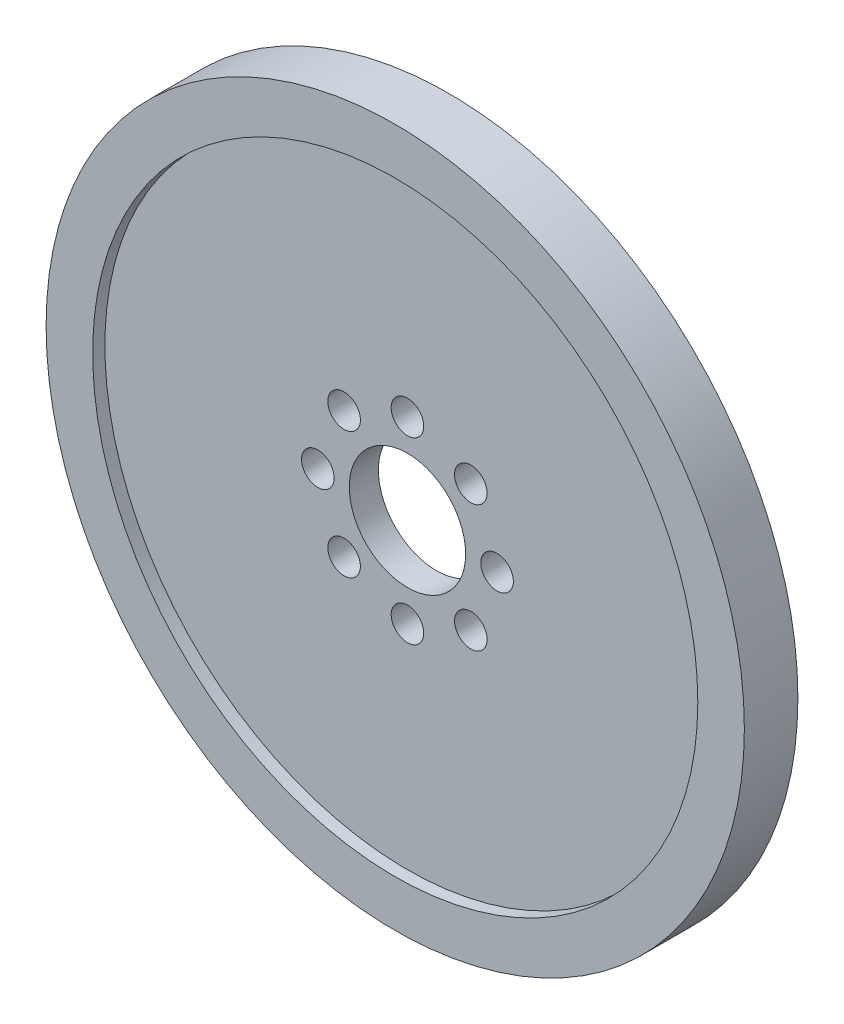
SolidWorks part; units mm, degrees
ref_plane "Front Plane" through (0, 0, 0) normal (0, 0, 1) x (1, 0, 0)
ref_plane "Top Plane" through (0, 0, 0) normal (0, 1, 0) x (1, 0, 0)
ref_plane "Right Plane" through (0, 0, 0) normal (1, 0, 0) x (0, 0, -1)
sketch "Sketch1" plane through (0, 0, 0) normal (0, 0, 1) x (1, 0, 0)
  circle A0 centre (0, 0) radius 38.1
  circle A1 centre (0, 0) radius 33.02
  dimension "D1" = 76.2
  dimension "D2" = 66.04
extrude "Boss-Extrude1" add sketch "Sketch1" along normal mid plane 5.842
sketch "Sketch3" plane through (0, 0, 0) normal (0, 0, 1) x (1, 0, 0)
  circle A0 centre (0, 0) radius 33.02
  circle A1 centre (0, 0) radius 6.35
  circle A2 centre (0, 9.779) radius 1.778
  circle A3 centre (6.9148, 6.9148) radius 1.778
  circle A4 centre (9.779, 0) radius 1.778
  circle A5 centre (6.9148, -6.9148) radius 1.778
  circle A6 centre (0, -9.779) radius 1.778
  circle A7 centre (-6.9148, -6.9148) radius 1.778
  circle A8 centre (-9.779, 0) radius 1.778
  circle A9 centre (-6.9148, 6.9148) radius 1.778
  dimension "D1" = 12.7
  dimension "D2" = 3.556
  dimension "D5" = 66.04
  dimension "D3" = 9.779
  dimension "D4" = 8
extrude "Boss-Extrude2" add sketch "Sketch3" along normal mid plane 3.175
